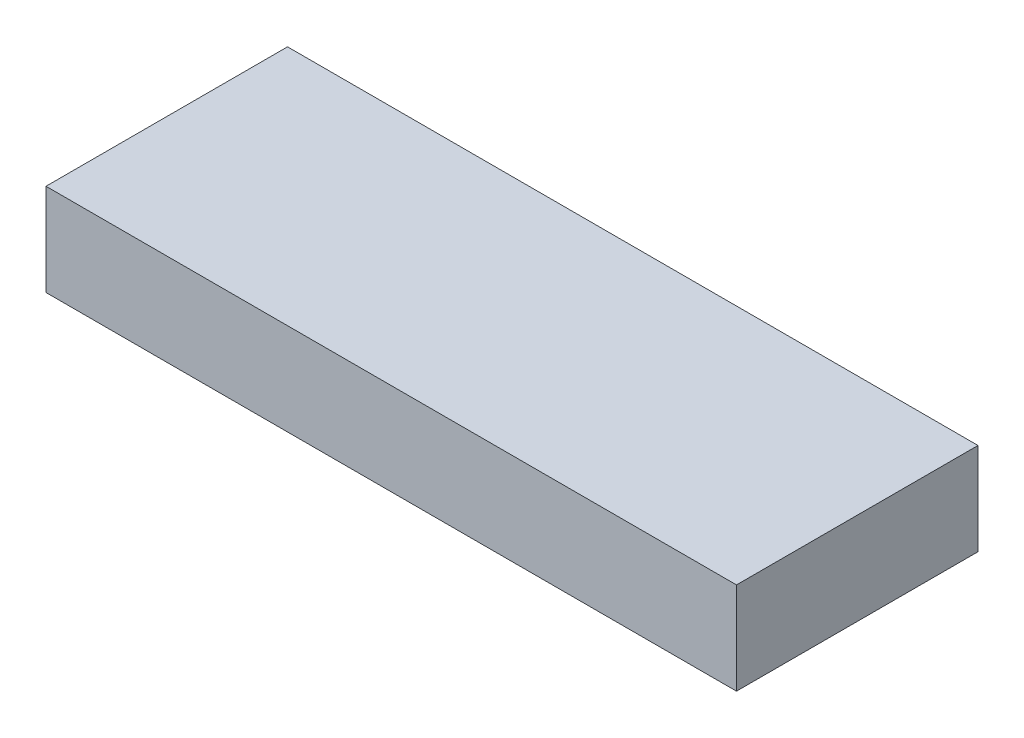
SolidWorks part; units mm, degrees
material "AISI 1020"
ref_plane "Front Plane" through (0, 0, 0) normal (0, 0, 1) x (1, 0, 0)
ref_plane "Top Plane" through (0, 0, 0) normal (0, 1, 0) x (1, 0, 0)
ref_plane "Right Plane" through (0, 0, 0) normal (1, 0, 0) x (0, 0, -1)
sketch "Sketch1" plane through (0, 0, 0) normal (0, 1, 0) x (1, 0, 0)
  line L1 (0, 0) -> (47.63, 0)
  line L2 (0, 0) -> (0, 16.66)
  line L3 (0, 16.66) -> (47.63, 16.66)
  line L4 (47.63, 0) -> (47.63, 16.66)
  dimension "D1" = 47.63
  dimension "D2" = 16.66
extrude "Boss-Extrude1" add sketch "Sketch1" along normal blind 6.35
